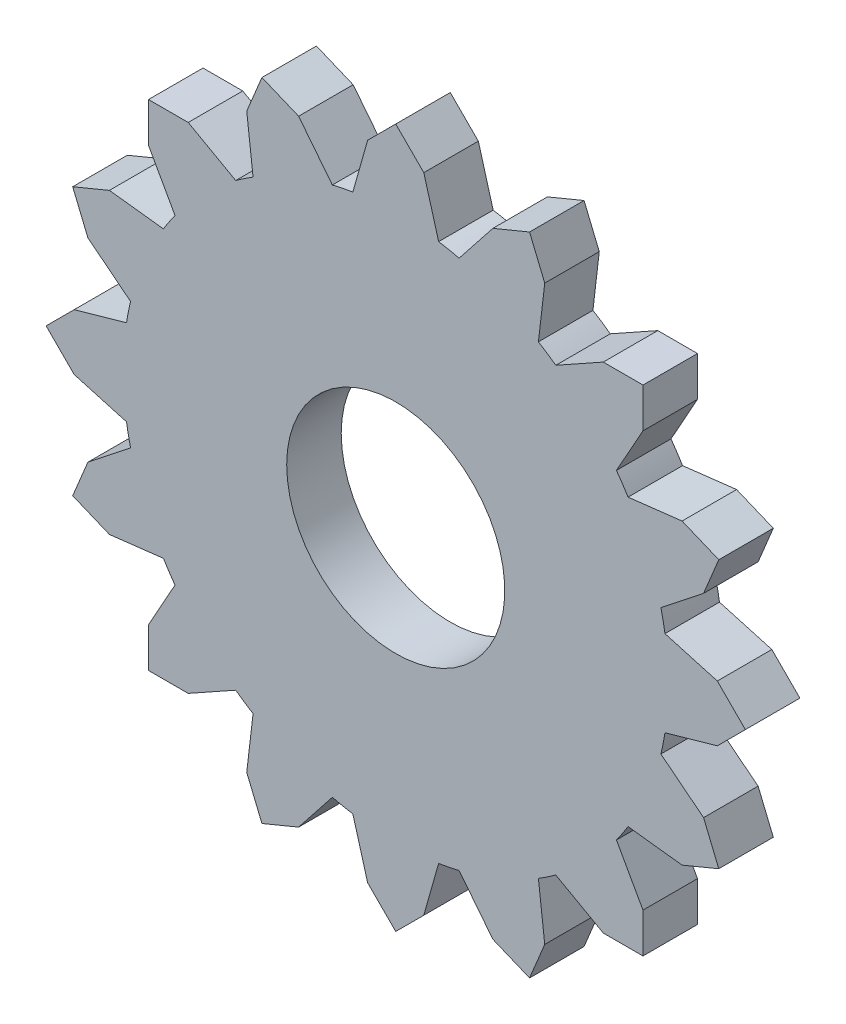
SolidWorks part; units mm, degrees
ref_plane "Front Plane" through (0, 0, 0) normal (0, 0, 1) x (1, 0, 0)
ref_plane "Top Plane" through (0, 0, 0) normal (0, 1, 0) x (1, 0, 0)
ref_plane "Right Plane" through (0, 0, 0) normal (1, 0, 0) x (0, 0, -1)
sketch "Sketch1" plane through (0, 0, 0) normal (0, 0, 1) x (1, 0, 0)
  line L0 (17.812, 56.458) -> (11.6265, 48.6295)
  line L1 (0, 64.1262) -> (5.1494, 58.9767)
  line L2 (5.1494, 58.9767) -> (7.8682, 49.377)
  line L3 (-5.1494, 58.9767) -> (-7.8682, 49.377)
  line L4 (0, 64.1262) -> (-5.1494, 58.9767)
  line L5 (24.54, 59.2448) -> (17.812, 56.458)
  line L6 (24.54, 59.2448) -> (27.3269, 52.5168)
  line L7 (27.3269, 52.5168) -> (26.1651, 42.6074)
  line L8 (38.0617, 45.344) -> (29.3512, 40.4785)
  line L9 (45.344, 45.344) -> (38.0617, 45.344)
  line L10 (45.344, 45.344) -> (45.344, 38.0617)
  line L11 (45.344, 38.0617) -> (40.4785, 29.3512)
  line L12 (52.5168, 27.3269) -> (42.6074, 26.1651)
  line L13 (59.2448, 24.54) -> (52.5168, 27.3269)
  line L14 (59.2448, 24.54) -> (56.458, 17.812)
  line L15 (56.458, 17.812) -> (48.6295, 11.6265)
  line L16 (58.9767, 5.1494) -> (49.377, 7.8682)
  line L17 (64.1262, 0) -> (58.9767, 5.1494)
  line L18 (64.1262, 0) -> (58.9767, -5.1494)
  line L19 (58.9767, -5.1494) -> (49.377, -7.8682)
  line L20 (56.458, -17.812) -> (48.6295, -11.6265)
  line L21 (59.2448, -24.54) -> (56.458, -17.812)
  line L22 (59.2448, -24.54) -> (52.5168, -27.3269)
  line L23 (52.5168, -27.3269) -> (42.6074, -26.1651)
  line L24 (45.344, -38.0617) -> (40.4785, -29.3512)
  line L25 (45.344, -45.344) -> (45.344, -38.0617)
  line L26 (45.344, -45.344) -> (38.0617, -45.344)
  line L27 (38.0617, -45.344) -> (29.3512, -40.4785)
  line L28 (27.3269, -52.5168) -> (26.1651, -42.6074)
  line L29 (24.54, -59.2448) -> (27.3269, -52.5168)
  line L30 (24.54, -59.2448) -> (17.812, -56.458)
  line L31 (17.812, -56.458) -> (11.6265, -48.6295)
  line L32 (5.1494, -58.9767) -> (7.8682, -49.377)
  line L33 (0, -64.1262) -> (5.1494, -58.9767)
  line L34 (0, -64.1262) -> (-5.1494, -58.9767)
  line L35 (-5.1494, -58.9767) -> (-7.8682, -49.377)
  line L36 (-17.812, -56.458) -> (-11.6265, -48.6295)
  line L37 (-24.54, -59.2448) -> (-17.812, -56.458)
  line L38 (-24.54, -59.2448) -> (-27.3269, -52.5168)
  line L39 (-27.3269, -52.5168) -> (-26.1651, -42.6074)
  line L40 (-38.0617, -45.344) -> (-29.3512, -40.4785)
  line L41 (-45.344, -45.344) -> (-38.0617, -45.344)
  line L42 (-45.344, -45.344) -> (-45.344, -38.0617)
  line L43 (-45.344, -38.0617) -> (-40.4785, -29.3512)
  line L44 (-52.5168, -27.3269) -> (-42.6074, -26.1651)
  line L45 (-59.2448, -24.54) -> (-52.5168, -27.3269)
  line L46 (-59.2448, -24.54) -> (-56.458, -17.812)
  line L47 (-56.458, -17.812) -> (-48.6295, -11.6265)
  line L48 (-58.9767, -5.1494) -> (-49.377, -7.8682)
  line L49 (-64.1262, 0) -> (-58.9767, -5.1494)
  line L50 (-64.1262, 0) -> (-58.9767, 5.1494)
  line L51 (-58.9767, 5.1494) -> (-49.377, 7.8682)
  line L52 (-56.458, 17.812) -> (-48.6295, 11.6265)
  line L53 (-59.2448, 24.54) -> (-56.458, 17.812)
  line L54 (-59.2448, 24.54) -> (-52.5168, 27.3269)
  line L55 (-52.5168, 27.3269) -> (-42.6074, 26.1651)
  line L56 (-45.344, 38.0617) -> (-40.4785, 29.3512)
  line L57 (-45.344, 45.344) -> (-45.344, 38.0617)
  line L58 (-45.344, 45.344) -> (-38.0617, 45.344)
  line L59 (-38.0617, 45.344) -> (-29.3512, 40.4785)
  line L60 (-27.3269, 52.5168) -> (-26.1651, 42.6074)
  line L61 (-24.54, 59.2448) -> (-27.3269, 52.5168)
  line L62 (-24.54, 59.2448) -> (-17.812, 56.458)
  line L63 (-17.812, 56.458) -> (-11.6265, 48.6295)
  arc A0 (-40.4785, 29.3512) -> (-42.6074, 26.1651) centre (0, 0) ccw
  arc A1 (-26.1651, 42.6074) -> (-29.3512, 40.4785) centre (0, 0) ccw
  arc A2 (-7.8682, 49.377) -> (-11.6265, 48.6295) centre (0, 0) ccw
  arc A3 (11.6265, 48.6295) -> (7.8682, 49.377) centre (0, 0) ccw
  arc A4 (29.3512, 40.4785) -> (26.1651, 42.6074) centre (0, 0) ccw
  arc A5 (-48.6295, 11.6265) -> (-49.377, 7.8682) centre (0, 0) ccw
  arc A6 (-49.377, -7.8682) -> (-48.6295, -11.6265) centre (0, 0) ccw
  arc A7 (42.6074, 26.1651) -> (40.4785, 29.3512) centre (0, 0) ccw
  arc A8 (49.377, 7.8682) -> (48.6295, 11.6265) centre (0, 0) ccw
  arc A9 (48.6295, -11.6265) -> (49.377, -7.8682) centre (0, 0) ccw
  arc A10 (40.4785, -29.3512) -> (42.6074, -26.1651) centre (0, 0) ccw
  arc A11 (26.1651, -42.6074) -> (29.3512, -40.4785) centre (0, 0) ccw
  arc A12 (-11.6265, -48.6295) -> (-7.8682, -49.377) centre (0, 0) ccw
  arc A13 (7.8682, -49.377) -> (11.6265, -48.6295) centre (0, 0) ccw
  arc A14 (-29.3512, -40.4785) -> (-26.1651, -42.6074) centre (0, 0) ccw
  arc A15 (-42.6074, -26.1651) -> (-40.4785, -29.3512) centre (0, 0) ccw
  point P85 (0, 0)
  dimension "D1" = 16
extrude "Boss-Extrude2" add sketch "Sketch1" along normal blind 10 contours L48 A6 L47 L46 L45 L44 A15 L43 L42 L41 L40 A14 L39 L38 L37 L36 A12 L35 L34 L33 L32 A13 L31 L30 L29 L28 A11 L27 L26 L25 L24 A10 L23 L22 L21 L20 A9 L19 L18 L17 L16 A8 L15 L14 L13 L12 A7 L11 L10 L9 L8 A4 L7 L6 L5 L0 A3 L2 L1 L4 L3 A2 L63 L62 L61 L60 A1 L59 L58 L57 L56 A0 L55 L54 L53 L52 A5 L51 L50 L49
sketch "Sketch2" plane through (0, 0, 0) normal (0, 0, -1) x (-1, 0, 0)
  circle A0 centre (0, 0) radius 20
extrude "Cut-Extrude1" cut sketch "Sketch2" against normal blind 10
